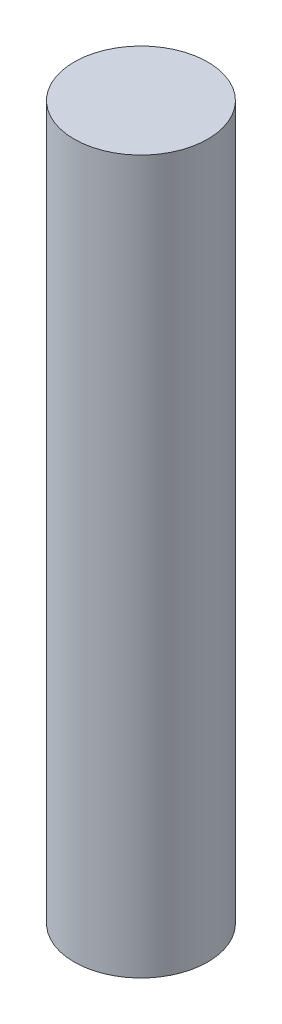
SolidWorks part; units mm, degrees
ref_plane "Front Plane" through (0, 0, 0) normal (0, 0, 1) x (1, 0, 0)
ref_plane "Top Plane" through (0, 0, 0) normal (0, 1, 0) x (1, 0, 0)
ref_plane "Right Plane" through (0, 0, 0) normal (1, 0, 0) x (0, 0, -1)
sketch "Sketch1" plane through (0, 0, 0) normal (0, 1, 0) x (1, 0, 0)
  circle A0 centre (0, 0) radius 1.5
extrude "Boss-Extrude1" add sketch "Sketch1" along normal blind 16
